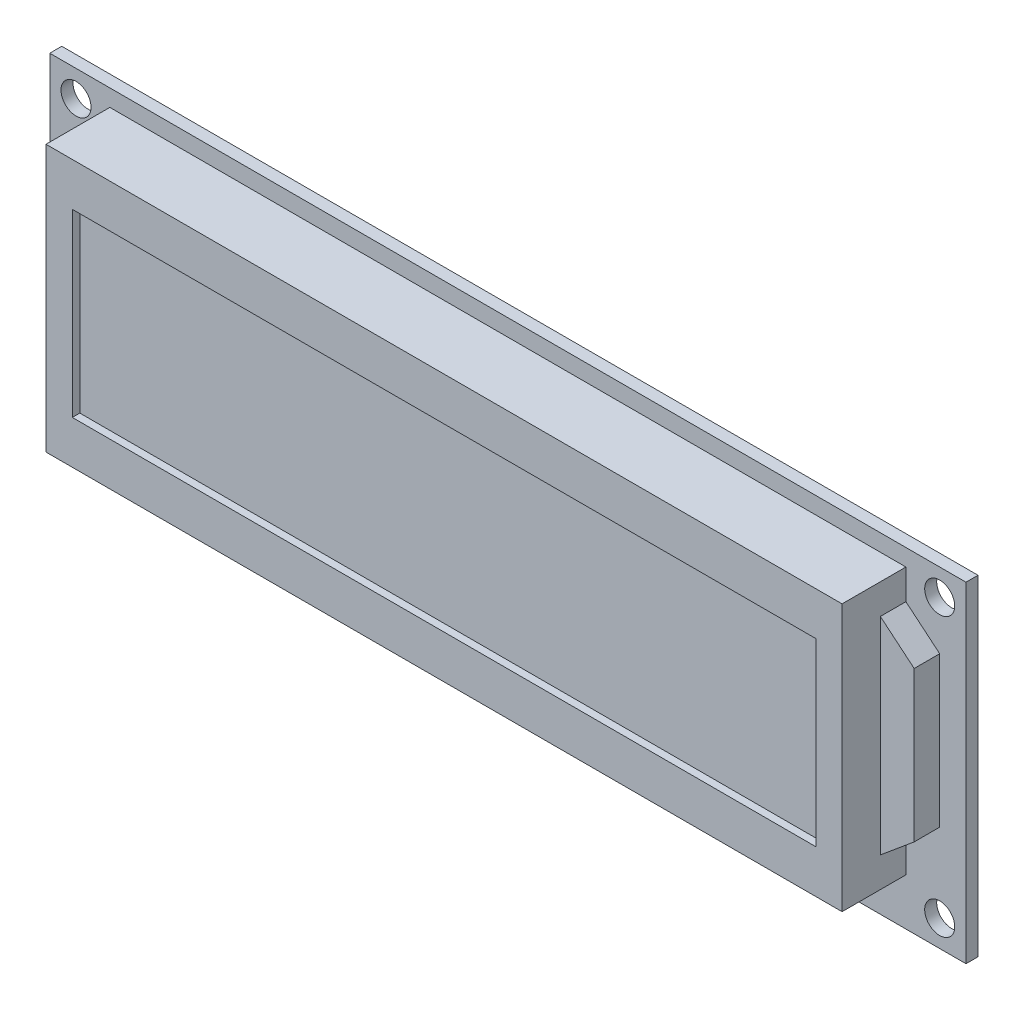
SolidWorks part; units mm, degrees
ref_plane "Front Plane" through (0, 0, 0) normal (0, 0, 1) x (1, 0, 0)
ref_plane "Top Plane" through (0, 0, 0) normal (0, 1, 0) x (1, 0, 0)
ref_plane "Right Plane" through (0, 0, 0) normal (1, 0, 0) x (0, 0, -1)
sketch "Sketch1" plane through (0, 0, 0) normal (0, 0, 1) x (1, 0, 0)
  line L0 (0, 22) -> (0, -22) construction
  line L1 (61, -22) -> (-61, -22)
  line L2 (61, -22) -> (61, 22)
  line L3 (61, 22) -> (-61, 22)
  line L4 (-61, -22) -> (-61, 22)
  line L5 (61, -22) -> (-61, 22) construction
  line L6 (61, 22) -> (-61, -22) construction
  line L7 (-61, 0) -> (61, 0) construction
  circle A0 centre (-57.5, 18.5) radius 2
  circle A1 centre (-57.5, -18.5) radius 2
  circle A2 centre (57.5, 18.5) radius 2
  circle A3 centre (57.5, -18.5) radius 2
  point P0 (0, 0)
  point P16 (0, 0)
  dimension "D3" = 4
  dimension "D1" = 122
  dimension "D2" = 44
  dimension "D4" = 37
  dimension "D5" = 115
extrude "Boss-Extrude1" add sketch "Sketch1" along normal blind 1.6
sketch "Sketch2" plane through (0, 0, 1.6) normal (0, 0, 1) x (1, 0, 0)
  line L0 (61, 22) -> (-61, 22) construction
  line L1 (53, -15.75) -> (-53, -15.75)
  line L2 (53, -15.75) -> (53, 19.75)
  line L3 (53, 19.75) -> (-53, 19.75)
  line L4 (-53, -15.75) -> (-53, 19.75)
  line L5 (53, -15.75) -> (-53, 19.75) construction
  line L6 (53, 19.75) -> (-53, -15.75) construction
  line L7 (61, -22) -> (61, 22) construction
  point P0 (0, 2)
  point P6 (0, 0)
  point P7 (0, 0)
  dimension "D1" = 106
  dimension "D2" = 35.5
  dimension "D3" = 2.25
  dimension "D4" = 8
extrude "Boss-Extrude2" add sketch "Sketch2" along normal blind 8.5
sketch "Sketch4" plane through (0, 0, 10.1) normal (0, 0, 1) x (1, 0, 0)
  line L0 (-53, 19.75) -> (53, -15.75) construction
  line L1 (49.5, -10) -> (-49.5, -10)
  line L2 (49.5, -10) -> (49.5, 14)
  line L3 (49.5, 14) -> (-49.5, 14)
  line L4 (-49.5, -10) -> (-49.5, 14)
  line L5 (49.5, -10) -> (-49.5, 14) construction
  line L6 (49.5, 14) -> (-49.5, -10) construction
  line L7 (-53, -15.75) -> (53, 19.75) construction
  point P0 (0, 2)
  point P14 (0, 2)
  point P15 (0, 0)
  point P16 (0, 0)
  dimension "D1" = 99
  dimension "D2" = 24
extrude "Cut-Extrude1" cut sketch "Sketch4" against normal blind 1
sketch "Sketch5" plane through (0, 0, 1.6) normal (0, 0, 1) x (1, 0, 0)
  line L0 (53, -15.75) -> (53, 19.75) construction
  line L1 (57.5, 2) -> (53, 2) construction
  line L2 (53, 15.75) -> (53, -11.75)
  line L3 (-49.5, 2) -> (49.5, 2) construction
  line L4 (57.5, 12) -> (57.5, -8)
  line L5 (53, -11.75) -> (57.5, -8)
  line L6 (53, 15.75) -> (57.5, 12)
  line L7 (-49.5, 14) -> (-49.5, -10) construction
  line L8 (49.5, -10) -> (49.5, 14) construction
  point P3 (53, 2)
  point P6 (57.5, 2)
  dimension "D1" = 4.5
  dimension "D2" = 27.5
  dimension "D3" = 20
extrude "Boss-Extrude3" add sketch "Sketch5" along normal blind 3.4
